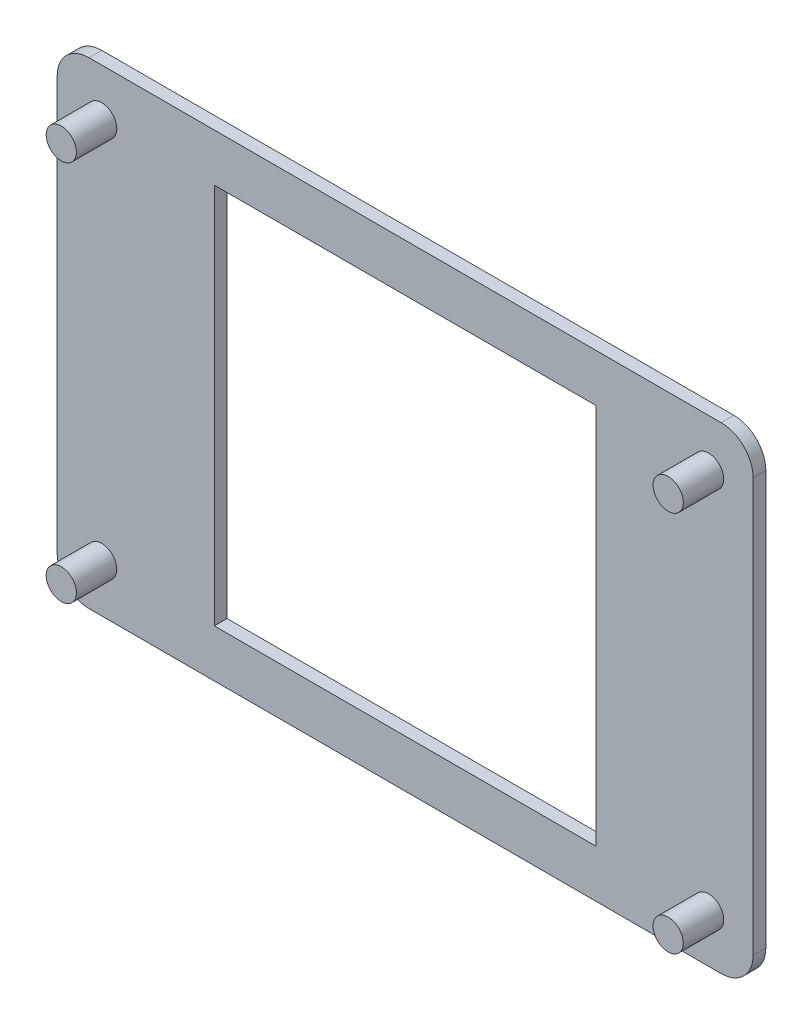
SolidWorks part; units mm, degrees
ref_plane "Front Plane" through (0, 0, 0) normal (0, 0, 1) x (1, 0, 0)
ref_plane "Top Plane" through (0, 0, 0) normal (0, 1, 0) x (1, 0, 0)
ref_plane "Right Plane" through (0, 0, 0) normal (1, 0, 0) x (0, 0, -1)
sketch "Sketch1" plane through (0, 0, 0) normal (0, 0, 1) x (1, 0, 0)
  line L1 (0, 0) -> (109.3978, 0)
  line L2 (0, 0) -> (0, 75)
  line L3 (0, 75) -> (109.3978, 75)
  line L4 (109.3978, 0) -> (109.3978, 75)
  dimension "D1" = 109.3978
  dimension "D2" = 75
extrude "Boss-Extrude1" add sketch "Sketch1" along normal blind 2
sketch "Sketch2" plane through (0, 0, 2) normal (0, 0, 1) x (1, 0, 0)
  line L0 (54.6989, 75) -> (54.6989, 0) construction
  line L1 (109.3978, 75) -> (0, 75) construction
  line L2 (0, 0) -> (109.3978, 0) construction
  line L3 (0, 37.5) -> (109.3978, 37.5) construction
  line L4 (0, 75) -> (0, 0) construction
  line L5 (109.3978, 0) -> (109.3978, 75) construction
  circle A0 centre (6.9977, 67.4974) radius 2.375
  circle A1 centre (102.4001, 67.4974) radius 2.375
  circle A2 centre (102.4001, 7.5026) radius 2.375
  circle A3 centre (6.9977, 7.5026) radius 2.375
  dimension "D1" = 4.75
  dimension "D2" = 29.9974
  dimension "D3" = 47.7012
extrude "Boss-Extrude2" add sketch "Sketch2" along normal blind 6.35
sketch "Sketch3" plane through (0, 0, 2) normal (0, 0, 1) x (1, 0, 0)
  line L0 (54.6989, 75) -> (54.6989, 0) construction
  line L1 (109.3978, 75) -> (0, 75) construction
  line L2 (0, 0) -> (109.3978, 0) construction
  line L3 (0, 37.5) -> (109.3978, 37.5) construction
  line L4 (0, 75) -> (0, 0) construction
  line L5 (109.3978, 0) -> (109.3978, 75) construction
  line L7 (24.6989, 7.5) -> (84.6989, 7.5)
  line L8 (24.6989, 7.5) -> (24.6989, 67.5)
  line L9 (24.6989, 67.5) -> (84.6989, 67.5)
  line L10 (84.6989, 7.5) -> (84.6989, 67.5)
  line L11 (24.6989, 7.5) -> (84.6989, 67.5) construction
  line L12 (24.6989, 67.5) -> (84.6989, 7.5) construction
  point P12 (54.6989, 37.5)
  dimension "D1" = 60
  dimension "D2" = 60
extrude "Cut-Extrude1" cut sketch "Sketch3" against normal up to next
fillet "Fillet1" radius 5 4 edges at (109.3978, 75, 1) (109.3978, 0, 1) (0, 0, 1) (0, 75, 1)
